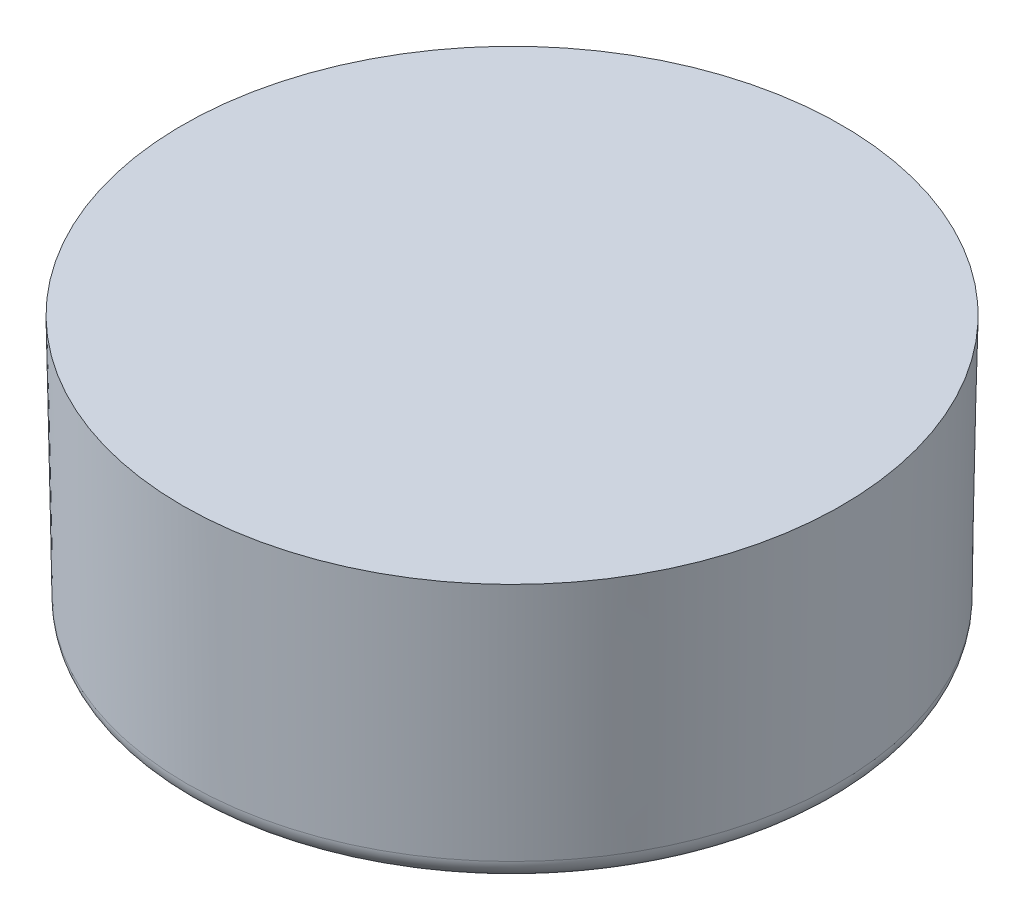
SolidWorks part; units mm, degrees
material "CA"
ref_plane "Front Plane" through (0, 0, 0) normal (0, 0, 1) x (1, 0, 0)
ref_plane "Top Plane" through (0, 0, 0) normal (0, 1, 0) x (1, 0, 0)
ref_plane "Right Plane" through (0, 0, 0) normal (1, 0, 0) x (0, 0, -1)
sketch "Sketch1" plane through (0, 0, 0) normal (0, 1, 0) x (1, 0, 0)
  circle A0 centre (0, 0) radius 7.9375
  dimension "D1" = 15.875
extrude "Boss-Extrude1" add sketch "Sketch1" against normal blind 6.35 draft 1
sketch "Sketch6" plane through (0, 0, 0) normal (0, 0, 1) x (1, 0, 0)
  line L0 (0, 0) -> (0, -2.413) construction
  line L1 (0, -2.413) -> (-7.112, -9.525)
  line L2 (0, -2.413) -> (7.112, -9.525)
  line L3 (-7.112, -9.525) -> (7.112, -9.525)
  line L5 (7.9375, 0) -> (-7.9375, 0) construction
  dimension "D1" = 2.413
  dimension "D2" = 90
  dimension "D3" = 9.525
extrude "Cut-Extrude3" cut sketch "Sketch6" against normal through all
pattern_circular "CirPattern3" count 9 over 360 about axis through (0, 0, 0) along (0, 1, 0) of "Cut-Extrude3"
sketch "Sketch7" plane through (0, 0, 0) normal (0, 1, 0) x (1, 0, 0)
  circle A1 centre (0, 0) radius 7.9375
  circle A2 centre (0, 0) radius 7.9375
  circle A3 centre (0, 0) radius 5.5245
  circle A4 centre (0, 0) radius 5.5245
  dimension "D1" = 0
  dimension "D2" = 2.413
extrude "Boss-Extrude3" add sketch "Sketch7" against normal blind 6.35 draft 1
draft "Draft1" type of draft neutral plane draft angle 10 faces to draft 1 face at (0, -6.35, 5.6353) neutral plane through (0, 0, 0) neutral plane normal (0, 1, 0) reverse direction yes parameters "D1"=10
fillet "Fillet2" radius 0.508 2 edges at (0, -6.35, 7.8267) (0, -6.35, 6.6442)
sketch "Sketch8" plane through (0, 0, 0) normal (1, 0, 0) x (0, 0, -1)
  line L1 (-6.3318, -4.5786) -> (-6.5702, -5.9302) construction
  line L2 (-2.975, -2.413) -> (0, -2.413) construction
  line L3 (-5.8001, -2.413) -> (-5.8001, -6.7202)
  line L4 (-6.5702, -5.9302) -> (-6.5702, -6.7202)
  line L5 (-6.5702, -6.7202) -> (-5.8001, -6.7202)
  line L6 (-5.95, -2.413) -> (-6.5702, -5.9302)
  arc A0 (-5.95, -2.413) -> (-5.8001, -2.413) centre (-5.875, -2.4262) cw
  dimension "D1" = 0.7701
  dimension "D2" = 0.79
revolve "Cut-Revolve1" cut sketch "Sketch8" angle 360 about L0
sketch "Sketch11 - OFFSET .005" plane through (0, 0, 0) normal (0, 1, 0) x (1, 0, 0)
  circle A1 centre (0, 0) radius 8.0645
  circle A2 centre (0, 0) radius 8.0645
  dimension "D1" = 0.127
